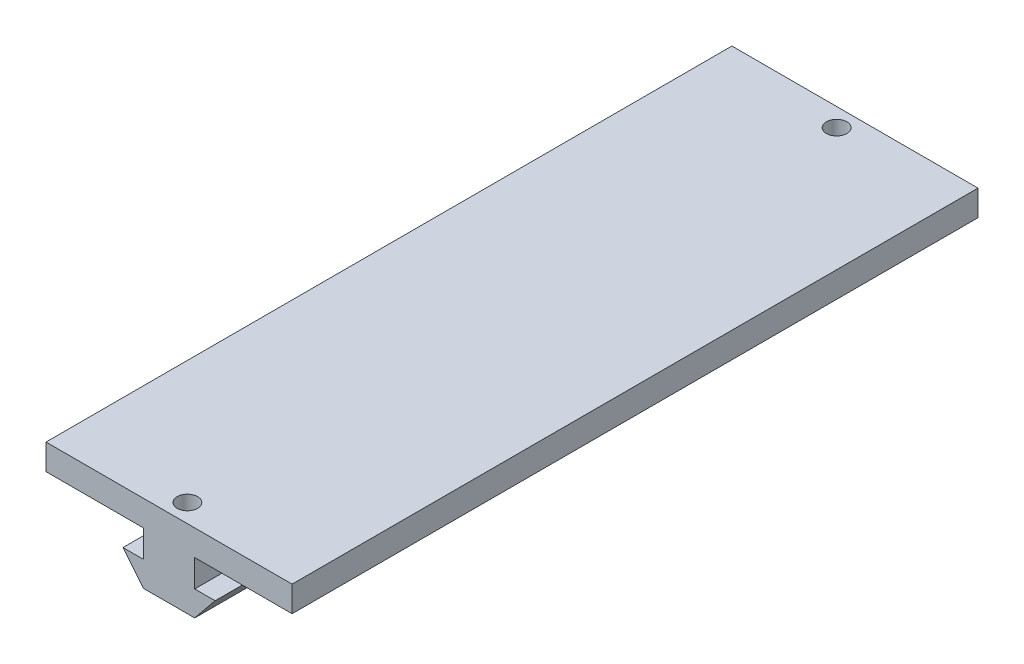
SolidWorks part; units mm, degrees
ref_plane "Front Plane" through (0, 0, 0) normal (0, 0, 1) x (1, 0, 0)
ref_plane "Top Plane" through (0, 0, 0) normal (0, 1, 0) x (1, 0, 0)
ref_plane "Right Plane" through (0, 0, 0) normal (1, 0, 0) x (0, 0, -1)
sketch "Sketch1" plane through (0, 0, 0) normal (0, 1, 0) x (1, 0, 0)
  line L1 (-23.5, -65.5) -> (23.5, -65.5)
  line L2 (-23.5, -65.5) -> (-23.5, 65.5)
  line L3 (-23.5, 65.5) -> (23.5, 65.5)
  line L4 (23.5, -65.5) -> (23.5, 65.5)
  line L5 (-23.5, -65.5) -> (23.5, 65.5) construction
  line L6 (-23.5, 65.5) -> (23.5, -65.5) construction
  point P0 (0, 0)
  dimension "D1" = 131
  dimension "D2" = 47
extrude "Boss-Extrude1" add sketch "Sketch1" along normal blind 4.9
sketch "Sketch3" plane through (0, 0, 65.5) normal (0, 0, 1) x (1, 0, 0)
  line L0 (-4.9, 0) -> (4.9, 0)
  line L1 (-23.5, 0) -> (23.5, 0) construction
  line L2 (4.9, 0) -> (4.9, -5.2)
  line L3 (4.9, -5.2) -> (8.8, -5.2)
  line L4 (8.8, -5.2) -> (4.9, -10)
  line L5 (4.9, -10) -> (-4.9, -10)
  line L6 (-4.9, -10) -> (-8.8, -5.2)
  line L7 (-8.8, -5.2) -> (-4.9, -5.2)
  line L8 (-4.9, -5.2) -> (-4.9, 0)
  line L9 (0, 4.9) -> (0, -15.5332) construction
  line L10 (-23.5, 4.9) -> (23.5, 4.9) construction
  dimension "D1" = 5.2
  dimension "D2" = 4.8
  dimension "D3" = 9.8
  dimension "D4" = 3.9
extrude "Boss-Extrude2" add sketch "Sketch3" against normal blind 50
sketch "Sketch2" plane through (0, 4.9, 0) normal (0, 1, 0) x (1, 0, 0)
  line L0 (-23.5, 0) -> (23.5, 0) construction
  line L1 (-23.5, 65.5) -> (-23.5, -65.5) construction
  line L2 (23.5, -65.5) -> (23.5, 65.5) construction
  circle A0 centre (0, 62) radius 1.95
  circle A1 centre (0, -62) radius 1.95
  dimension "D2" = 3.9
  dimension "D1" = 124
extrude "Cut-Extrude1" cut sketch "Sketch2" against normal blind 6
